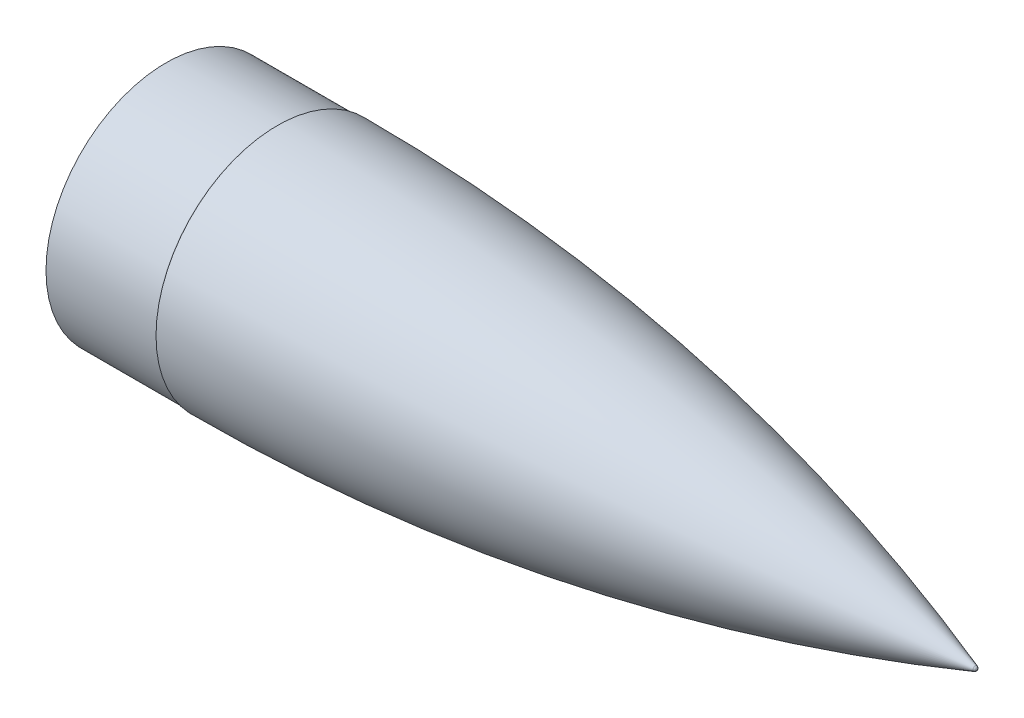
SolidWorks part; units mm, degrees
ref_plane "前基準面" through (0, 0, 0) normal (0, 0, 1) x (1, 0, 0)
ref_plane "上基準面" through (0, 0, 0) normal (0, 1, 0) x (1, 0, 0)
ref_plane "右基準面" through (0, 0, 0) normal (1, 0, 0) x (0, 0, -1)
sketch "草圖2" plane through (0, 0, 0) normal (0, 0, 1) x (1, 0, 0)
  line L0 (-558.8, 97) -> (-558.8, 96.88)
  line L1 (0, 0) -> (-3.5097, 0)
  line L3 (-711, 0) -> (126.4299, 0) construction
  line L4 (0, 26.965) -> (0, -35.3928) construction
  line L5 (-558.8, 97) -> (-39.4127, 97) construction
  line L7 (-647.8, 93.88) -> (-558.8, 93.88)
  line L8 (-647.8, 93.88) -> (-647.8, 95.88)
  line L9 (-647.8, 95.88) -> (-559.8, 95.88)
  line L10 (-558.8, 93.88) -> (-558.8, 93.4997)
  line L11 (-647.8, 93.88) -> (-558.8, 95.88) construction
  line L12 (-647.8, 95.88) -> (-558.8, 93.88) construction
  arc A1 (0, 0) -> (-1.3368, 1.8869) centre (-2, 0) ccw
  arc A2 (-1.3368, 1.8869) -> (-558.8, 97) centre (-558.8, -1584.2171) ccw
  arc A3 (-3.5097, 0) -> (-557.7994, 94.4997) centre (-558.8, -1584.2171) ccw
  arc A4 (-558.8, 96.88) -> (-559.8, 95.88) centre (-559.8, 96.88) cw
  arc A5 (-2.1658, -0.4717) -> (-558.8, 94.5) centre (-558.8, -1584.2171) ccw construction
  arc A6 (-557.7994, 94.4997) -> (-558.8, 93.4997) centre (-557.8, 93.4997) ccw
  point P4 (-603.3, 94.88)
  dimension "D3" = 2
  dimension "D5" = 1
  dimension "D9" = 1
  dimension "D1" = 97
  dimension "D2" = 558.8
  dimension "D6" = 89
  dimension "D7" = 191.76
  dimension "D8" = 187.76
  dimension "D4" = 2.5
revolve "旋轉1" add sketch "草圖2" angle 360 about L3
